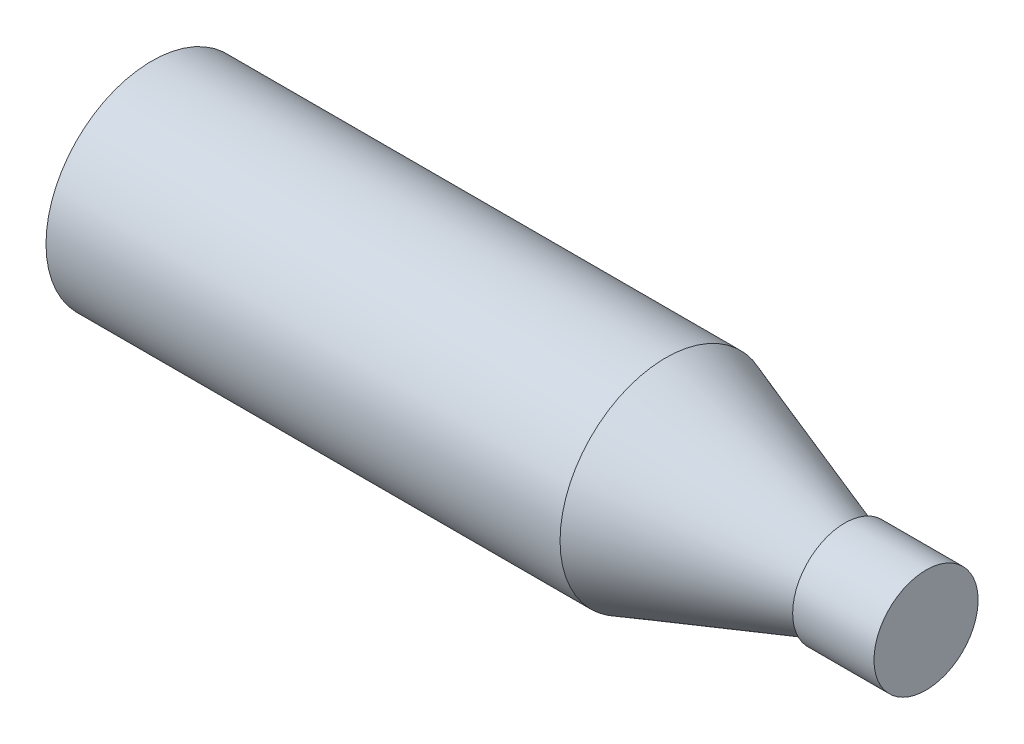
SolidWorks part; units mm, degrees
ref_plane "Спереди" through (0, 0, 0) normal (0, 0, 1) x (1, 0, 0)
ref_plane "Сверху" through (0, 0, 0) normal (0, 1, 0) x (1, 0, 0)
ref_plane "Справа" through (0, 0, 0) normal (1, 0, 0) x (0, 0, -1)
sketch "Эскиз1" plane through (0, 0, 0) normal (0, 0, 1) x (1, 0, 0)
  line L0 (-50.7749, 0) -> (101.9877, 0) construction
  line L1 (-50.7749, 0) -> (-50.7749, 32.5)
  line L2 (-50.7749, 32.5) -> (107.2251, 32.5)
  line L3 (107.2251, 32.5) -> (162.2251, 13.5)
  line L4 (162.2251, 13.5) -> (162.2251, 16)
  line L5 (162.2251, 16) -> (187.2251, 16)
  line L6 (187.2251, 16) -> (187.2251, 0)
  line L7 (-50.7749, 0) -> (187.2251, 0)
  point P8 (187.2251, 8)
  dimension "D1" = 65
  dimension "D2" = 27
  dimension "D3" = 32
  dimension "D4" = 25
  dimension "D5" = 238
  dimension "D6" = 80
revolve "Повернуть1" add sketch "Эскиз1" angle 360 about L0
